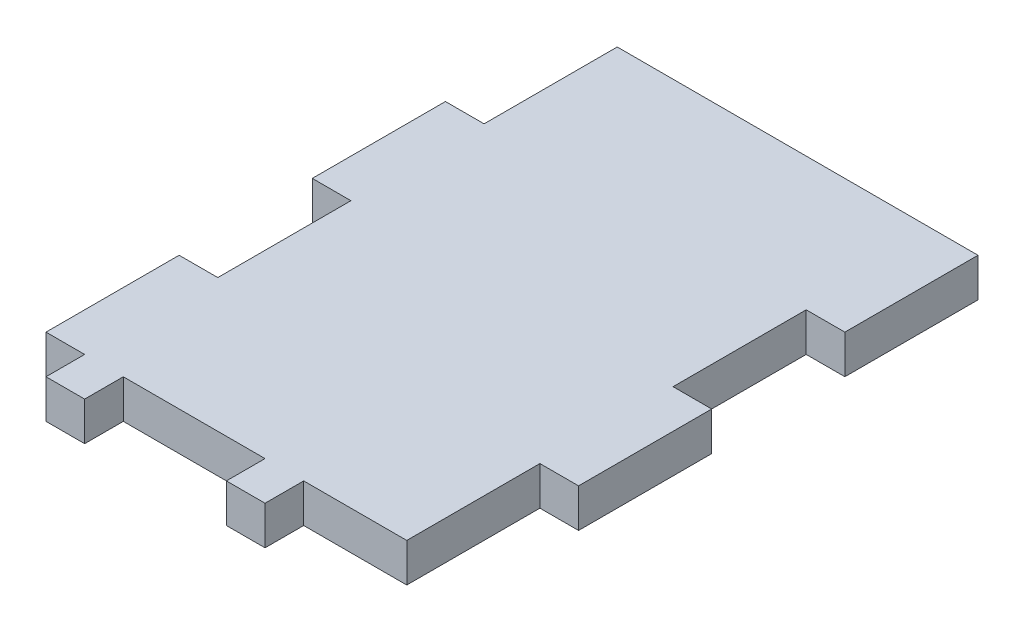
SolidWorks part; units mm, degrees
ref_plane "Front Plane" through (0, 0, 0) normal (0, 0, 1) x (1, 0, 0)
ref_plane "Top Plane" through (0, 0, 0) normal (0, 1, 0) x (1, 0, 0)
ref_plane "Right Plane" through (0, 0, 0) normal (1, 0, 0) x (0, 0, -1)
sketch "Sketch1" plane through (0, 0, 0) normal (0, 1, 0) x (1, 0, 0)
  line L0 (-21, 0) -> (-21, -15.5)
  line L1 (-21, 31) -> (21, 31)
  line L2 (-25.5, 15.5) -> (-25.5, 0)
  line L3 (16.5, -31) -> (4.5, -31)
  line L4 (-21, -31) -> (-21, -35.5)
  line L5 (0, -31) -> (0, -35.5)
  line L6 (16.5, -31) -> (16.5, -15.5)
  line L7 (-16.5, -31) -> (0, -31)
  line L8 (16.5, 0) -> (21, 0)
  line L9 (-21, -35.5) -> (-16.5, -35.5)
  line L12 (-16.5, -35.5) -> (-16.5, -31)
  line L17 (0, -35.5) -> (4.5, -35.5)
  line L20 (4.5, -35.5) -> (4.5, -31)
  line L27 (16.5, -15.5) -> (21, -15.5)
  line L30 (21, -15.5) -> (21, 0)
  line L34 (16.5, 0) -> (16.5, 15.5)
  line L35 (16.5, 15.5) -> (21, 15.5)
  line L38 (21, 15.5) -> (21, 31)
  line L40 (-21, 31) -> (-21, 15.5)
  line L43 (-25.5, 15.5) -> (-21, 15.5)
  line L47 (-25.5, 0) -> (-21, 0)
  line L51 (-21, -15.5) -> (-25.5, -15.5)
  line L53 (-21, -31) -> (-25.5, -31)
  line L55 (-25.5, -15.5) -> (-25.5, -31)
  dimension "D1" = 42
  dimension "D2" = 4.5
  dimension "D3" = 4.5
  dimension "D4" = 4.5
  dimension "D5" = 4.5
  dimension "D6" = 4.5
  dimension "D7" = 4.5
  dimension "D8" = 62
  dimension "D9" = 12
extrude "Boss-Extrude1" add sketch "Sketch1" along normal blind 4.5
